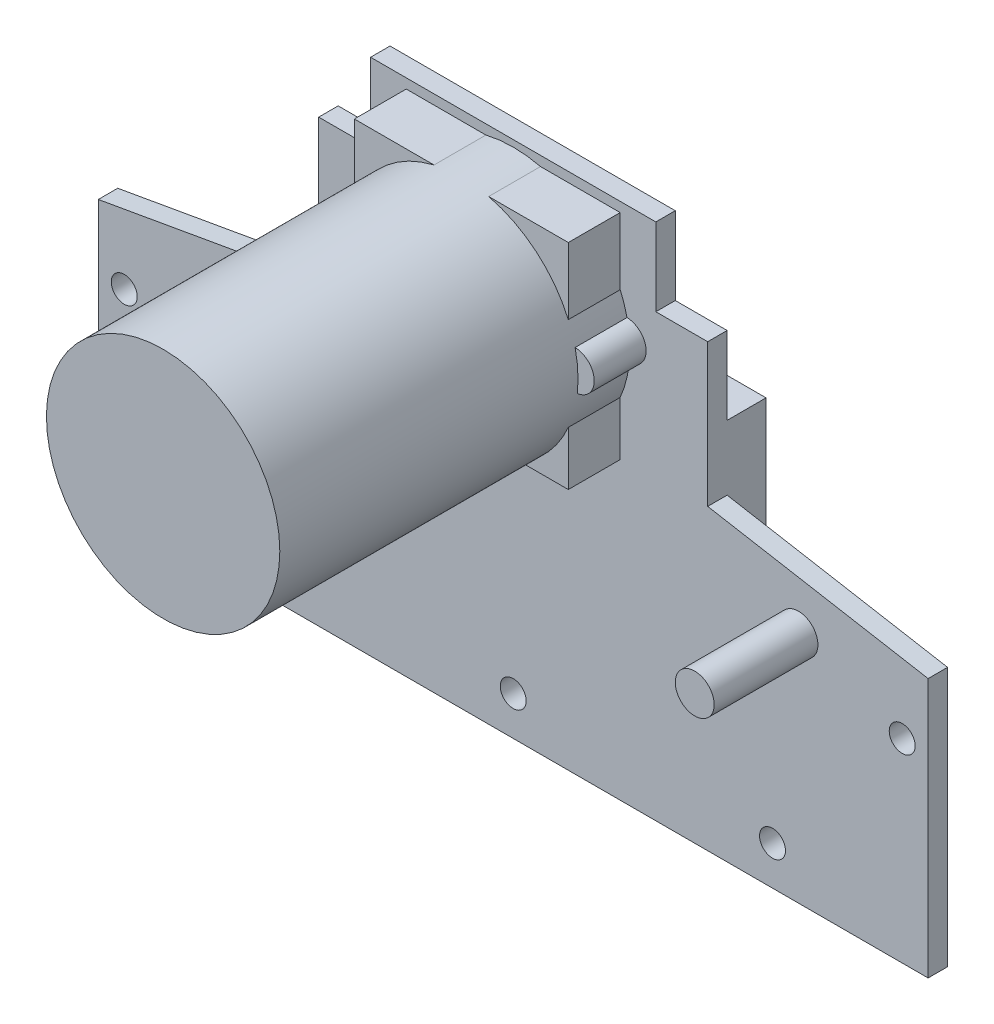
SolidWorks part; units mm, degrees
material "Nickel"
ref_plane "Front Plane" through (0, 0, 0) normal (0, 0, 1) x (1, 0, 0)
ref_plane "Top Plane" through (0, 0, 0) normal (0, 1, 0) x (1, 0, 0)
ref_plane "Right Plane" through (0, 0, 0) normal (1, 0, 0) x (0, 0, -1)
sketch "Sketch1" plane through (0, 0, 0) normal (0, 0, 1) x (1, 0, 0)
  line L0 (-32, 0) -> (32, 0)
  line L1 (-1015.4659, 23) -> (48984.5341, 23) construction
  line L2 (-15, 23) -> (15, 23)
  line L3 (-32, 0) -> (-32, 20)
  line L4 (-32, 20) -> (-15, 23)
  line L5 (32, 0) -> (32, 20)
  line L6 (32, 20) -> (15, 23)
  line L7 (-15, 23) -> (-15, 34)
  line L8 (-15, 34) -> (15, 34)
  line L9 (15, 34) -> (15, 23)
  line L10 (-1006.9308, 40) -> (48993.0692, 40) construction
  line L11 (-11, 40) -> (11, 40)
  line L12 (-11, 40) -> (-11, 34)
  line L13 (11, 40) -> (11, 34)
  line L14 (0, 34) -> (0, 40) construction
  dimension "D1" = 64
  dimension "D2" = 23
  dimension "D3" = 30
  dimension "D4" = 20
  dimension "D5" = 11
  dimension "D6" = 6
  dimension "D7" = 22
extrude "Boss-Extrude1" add sketch "Sketch1" along normal blind 1.5 contours L5 L6 L2 L4 L3 L0 | L9 L8 L7 L2 | L13 L11 L12 L8
sketch "Sketch2" plane through (0, 0, 1.5) normal (0, 0, 1) x (1, 0, 0)
  line L0 (-1024.4669, 3) -> (48975.5331, 3) construction
  line L1 (-32, 0) -> (32, 0) construction
  line L2 (-20, 3) -> (20, 3)
  line L3 (-32, 0) -> (-32, 20) construction
  line L4 (0, -997) -> (0, 49003) construction
  circle A0 centre (-20, 3) radius 1
  circle A1 centre (20, 3) radius 1
  circle A2 centre (0, 3) radius 1
  circle A3 centre (-30, 15) radius 1
  circle A4 centre (30, 15) radius 1
  dimension "D3" = 2
  dimension "D1" = 40
  dimension "D2" = 3
  dimension "D5" = 15
  dimension "D6" = 2
extrude "Cut-Extrude1" cut sketch "Sketch2" against normal blind 5
sketch "Sketch3" plane through (0, 0, 1.5) normal (0, 0, 1) x (1, 0, 0)
  line L0 (0, 40) -> (0, 0) construction
  line L1 (-11, 40) -> (11, 40) construction
  line L2 (-32, 0) -> (32, 0) construction
  line L4 (-8.5, 39) -> (8.5, 39)
  line L5 (-8.5, 39) -> (-8.5, 22)
  line L6 (-8.5, 22) -> (8.5, 22)
  line L7 (8.5, 39) -> (8.5, 22)
  circle A0 centre (0, 30.5) radius 9
  circle A1 centre (0, 30.5) radius 8.5
  dimension "D1" = 18
  dimension "D2" = 17
  dimension "D3" = 17
  dimension "D4" = 1
extrude "Boss-Extrude2" add sketch "Sketch3" along normal blind 27 contours A0
sketch "Sketch4" plane through (0, 0, 28.5) normal (0, 0, 1) x (1, 0, 0)
  circle A0 centre (0, 31) radius 9
sketch "Sketch5" plane through (0, 0, 0) normal (0, 0, -1) x (-1, 0, 0)
  line L0 (32, 0) -> (-32, 0) construction
  line L1 (-15, 7) -> (13, 7)
  line L2 (-15, 7) -> (-15, 28)
  line L3 (-15, 28) -> (13, 28)
  line L4 (13, 7) -> (13, 28)
  line L5 (32, 0) -> (32, 20) construction
  line L6 (15, 23) -> (15, 34) construction
  dimension "D1" = 28
  dimension "D2" = 19
  dimension "D3" = 30
  dimension "D4" = 7
extrude "Boss-Extrude3" add sketch "Sketch5" along normal blind 3
sketch "Sketch6" plane through (0, 0, 1.5) normal (0, 0, 1) x (1, 0, 0)
  line L0 (22, 18) -> (-22, 18) construction
  line L1 (0, 0) -> (0, 18) construction
  line L2 (-32, 0) -> (32, 0) construction
  circle A0 centre (22, 18) radius 1.5
  circle A1 centre (-22, 18) radius 1.5
  dimension "D2" = 3
  dimension "D1" = 44
  dimension "D3" = 18
extrude "Boss-Extrude4" add sketch "Sketch6" along normal blind 8
sketch "Sketch7" plane through (0, 0, 1.5) normal (0, 0, 1) x (1, 0, 0)
  line L0 (-10.25, 41.25) -> (-10.25, 20.75) construction
  line L1 (-8.25, 39.25) -> (8.25, 39.25)
  line L2 (-8.25, 39.25) -> (-8.25, 22.75)
  line L3 (-8.25, 22.75) -> (8.25, 22.75)
  line L4 (8.25, 39.25) -> (8.25, 22.75)
  line L5 (-8.25, 39.25) -> (8.25, 22.75) construction
  line L6 (-8.25, 22.75) -> (8.25, 39.25) construction
  line L7 (-10.25, 20.75) -> (10.25, 20.75) construction
  line L8 (10.25, 41.25) -> (10.25, 20.75) construction
  line L9 (-10.25, 41.25) -> (10.25, 41.25) construction
  circle A0 centre (0, 31) radius 9 construction
  circle A2 centre (-8.75, 31) radius 1.5
  circle A3 centre (8.75, 31) radius 1.5
  point P0 (0, 31)
  dimension "D3" = 3
  dimension "D1" = 16.5
  dimension "D2" = 2
extrude "Boss-Extrude5" add sketch "Sketch7" along normal blind 4 contours A2 | L2 L3 L4 L1 | A3
